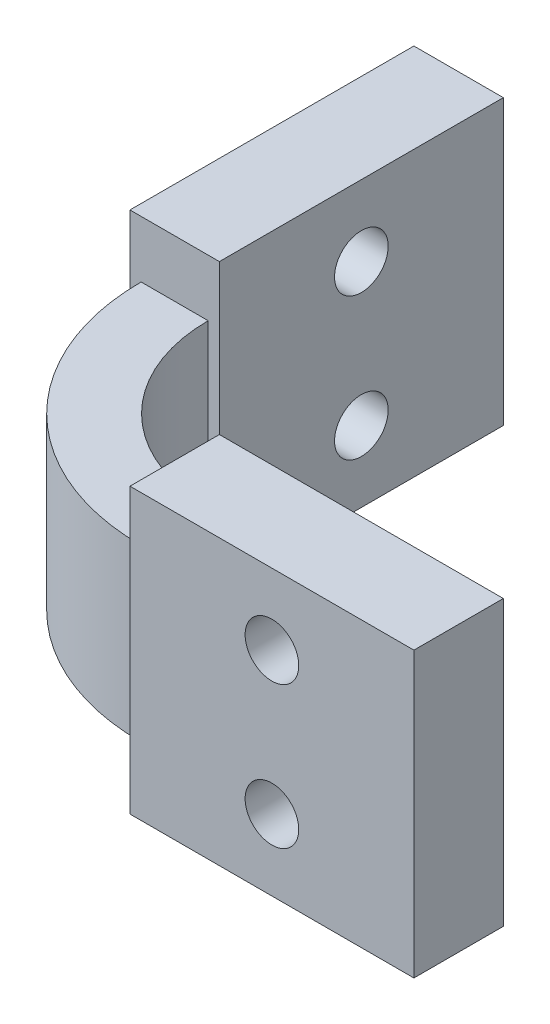
SolidWorks part; units mm, degrees
material "6061-T6 (SS)"
ref_plane "Front Plane" through (0, 0, 0) normal (0, 0, 1) x (1, 0, 0)
ref_plane "Top Plane" through (0, 0, 0) normal (0, 1, 0) x (1, 0, 0)
ref_plane "Right Plane" through (0, 0, 0) normal (1, 0, 0) x (0, 0, -1)
sketch "Sketch2" plane through (0, 0, 0) normal (0, 1, 0) x (1, 0, 0)
  line L0 (-3.246, -12.5472) -> (-3.246, 33.9472) construction
  line L1 (-3.746, 20.86) -> (0.254, 20.86)
  line L2 (-3.746, 20.86) -> (-3.746, 8.16)
  line L3 (-3.746, 8.16) -> (-3.246, 8.16)
  line L4 (0.254, 20.86) -> (0.254, 8.16)
  line L5 (6.954, 1.46) -> (19.654, 1.46)
  line L6 (6.954, 1.46) -> (6.954, 0.96)
  line L7 (6.954, -2.54) -> (19.654, -2.54)
  line L8 (19.654, 1.46) -> (19.654, -2.54)
  line L9 (-9.7938, -2.04) -> (28.7818, -2.04) construction
  line L10 (-0.246, 33.9472) -> (-0.246, -12.5472) construction
  line L11 (28.7818, 0.96) -> (-9.7938, 0.96) construction
  line L12 (-3.246, 10.7) -> (-0.246, 10.7) construction
  line L13 (9.494, 0.96) -> (9.494, -2.04) construction
  line L14 (-0.246, 8.16) -> (0.254, 8.16)
  line L15 (6.954, -2.04) -> (6.954, -2.54)
  arc A1 (-3.246, 8.16) -> (6.954, -2.04) centre (6.954, 8.16) ccw
  arc A2 (-0.246, 8.16) -> (6.954, 0.96) centre (6.954, 8.16) ccw
  point P18 (-3.246, 10.7)
  point P19 (-1.746, 10.7)
  point P20 (-1.746, 20.86)
  point P26 (9.494, 0.96)
  point P27 (9.494, -2.04)
  point P29 (-0.246, 10.7)
  point P31 (9.494, -0.54)
  point P34 (19.654, -0.54)
  dimension "D1" = 12.7
  dimension "D2" = 4
  dimension "D3" = 3
  dimension "D4" = 23.4
  dimension "D5" = 23.4
  dimension "D6" = 2.54
  dimension "D7" = 2.54
  dimension "D8" = 0.254
  dimension "D9" = 2.54
extrude "Boss-Extrude1" add sketch "Sketch2" along normal mid plane 7.62
sketch "Sketch3" plane through (0, 3.81, 0) normal (0, 1, 0) x (1, 0, 0)
  line L0 (6.954, -2.54) -> (19.654, -2.54) construction
  line L1 (19.654, -2.54) -> (19.654, 1.46) construction
  line L2 (19.654, 1.46) -> (6.954, 1.46) construction
  line L3 (0.254, 8.16) -> (0.254, 20.86) construction
  line L4 (-3.746, 20.86) -> (-3.746, 8.16) construction
  line L5 (0.254, 20.86) -> (-3.746, 20.86) construction
  line L6 (6.954, -2.54) -> (19.654, -2.54)
  line L7 (19.654, -2.54) -> (19.654, 1.46)
  line L8 (19.654, 1.46) -> (6.954, 1.46)
  line L9 (0.254, 8.16) -> (0.254, 20.86)
  line L10 (-3.746, 20.86) -> (-3.746, 8.16)
  line L11 (0.254, 20.86) -> (-3.746, 20.86)
  line L12 (-3.746, 8.16) -> (0.254, 8.16)
  line L13 (6.954, 1.46) -> (6.954, -2.54)
extrude "Boss-Extrude2" add sketch "Sketch3" along normal blind 2.54
mirror "Mirror1" about plane through (0, 0, 0) normal (0, 1, 0) of "Boss-Extrude2"
sketch "Sketch4" plane through (0.254, 0, 0) normal (1, 0, 0) x (0, 0, -1)
  line L0 (8.16, 6.35) -> (20.86, 6.35) construction
  line L1 (20.86, 0) -> (8.16, 0) construction
  line L2 (20.86, 6.35) -> (20.86, -6.35) construction
  line L3 (8.16, 6.35) -> (8.16, -6.35) construction
  line L4 (14.51, 0) -> (14.51, 6.35) construction
  point P0 (14.51, 3.175)
  point P3 (14.51, 6.35)
  point P10 (0, 0)
  point P13 (14.51, -3.175)
hole_wizard "M2 Clearance Hole1" positions "Sketch5" profile "Sketch6" hole size "M2" standard "ANSI Metric" end condition through all
sketch "Sketch5" plane through (0.254, 0, 0) normal (1, 0, 0) x (0, 0, -1)
  point P0 (14.51, 3.175)
  point P3 (14.51, -3.175)
sketch "Sketch6" plane through (0.254, 3.175, -14.51) normal (0, 1, 0) x (0, 0, -1)
  line L0 (0, 0) -> (0, 4)
  line L1 (0, 4) -> (1.2, 4)
  line L2 (1.2, 4) -> (1.2, 0)
  line L5 (1.2, 0) -> (0, 0)
  line L11 (0, -6.35) -> (0, 107.95) construction
  dimension "Thru Hole Dia." = 2.4
  dimension "Thru Hole Depth" = 4
sketch "Sketch7" plane through (0, 0, -1.46) normal (0, 0, -1) x (-1, 0, 0)
  line L0 (-6.954, 0) -> (-19.654, 0) construction
  line L1 (-6.954, 6.35) -> (-6.954, -6.35) construction
  line L2 (-19.654, 6.35) -> (-19.654, -6.35) construction
  line L3 (-13.304, 6.35) -> (-13.304, 0) construction
  line L4 (-19.654, 6.35) -> (-6.954, 6.35) construction
  point P0 (-13.304, 3.175)
  point P11 (-13.304, 0)
  point P12 (0, 0)
  point P13 (0, 0)
  point P14 (-13.304, -3.175)
hole_wizard "M2 Clearance Hole2" positions "Sketch8" profile "Sketch9" hole size "M2" standard "ANSI Metric" end condition through all
sketch "Sketch8" plane through (0, 0, -1.46) normal (0, 0, -1) x (-1, 0, 0)
  point P0 (-13.304, 3.175)
  point P3 (-13.304, -3.175)
sketch "Sketch9" plane through (13.304, 3.175, -1.46) normal (1, 0, 0) x (0, 1, 0)
  line L0 (0, 0) -> (0, 4)
  line L1 (0, 4) -> (1.2, 4)
  line L2 (1.2, 4) -> (1.2, 0)
  line L5 (1.2, 0) -> (0, 0)
  line L11 (0, -6.35) -> (0, 107.95) construction
  dimension "Thru Hole Dia." = 2.4
  dimension "Thru Hole Depth" = 4
